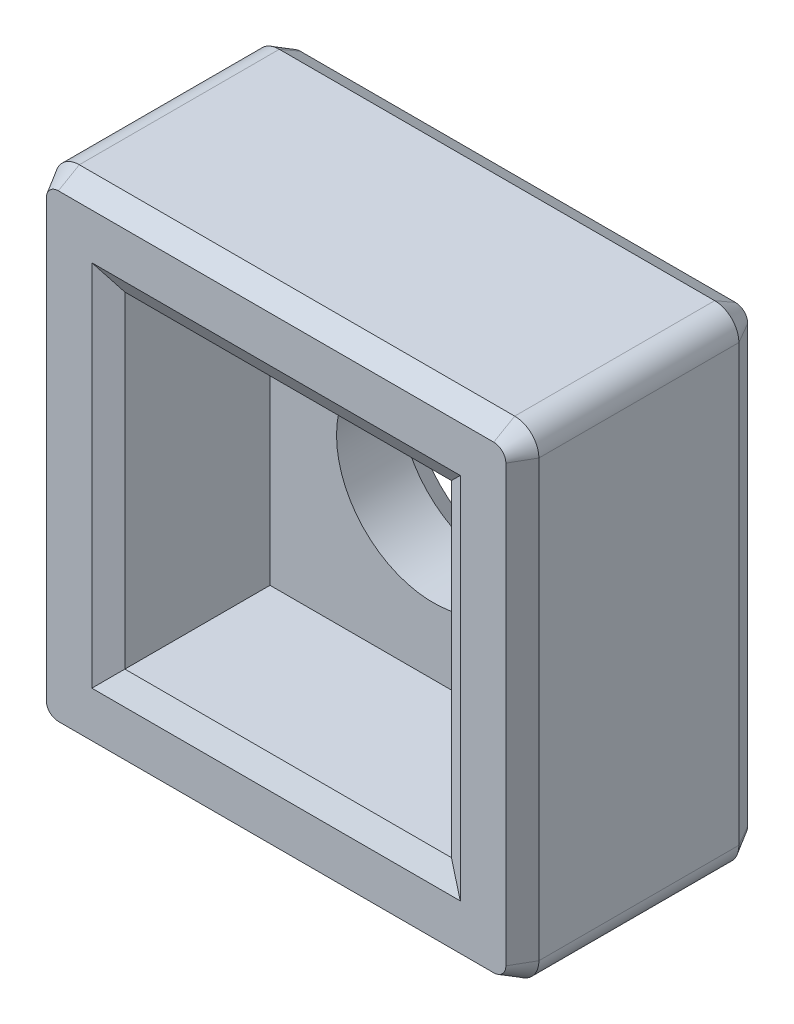
SolidWorks part; units mm, degrees
ref_plane "Front Plane" through (0, 0, 0) normal (0, 0, 1) x (1, 0, 0)
ref_plane "Top Plane" through (0, 0, 0) normal (0, 1, 0) x (1, 0, 0)
ref_plane "Right Plane" through (0, 0, 0) normal (1, 0, 0) x (0, 0, -1)
sketch "Sketch1" plane through (0, 0, 0) normal (0, 0, 1) x (1, 0, 0)
  line L0 (-4, -4) -> (4, 4) construction
  line L1 (-4, 4) -> (4, 4)
  line L2 (-4, 4) -> (-4, -4)
  line L3 (-4, -4) -> (4, -4)
  line L4 (4, 4) -> (4, -4)
  dimension "D1" = 8
extrude "Boss-Extrude1" add sketch "Sketch1" along normal blind 4
fillet "Fillet1" radius 0.4 4 edges at (-4, -4, 2) (4, -4, 2) (4, 4, 2) (-4, 4, 2)
sketch "Sketch3" plane through (0, 0, 0) normal (0, 0, -1) x (-1, 0, 0)
  circle A0 centre (0, 0) radius 1.6
  dimension "D1" = 3.2
extrude "Cut-Extrude1" cut sketch "Sketch3" against normal through all
sketch "Sketch4" plane through (0, 0, 4) normal (0, 0, 1) x (1, 0, 0)
  line L0 (2.7, 2.7) -> (-2.7, -2.7) construction
  line L1 (-2.7, 2.7) -> (2.7, 2.7)
  line L2 (-2.7, 2.7) -> (-2.7, -2.7)
  line L3 (-2.7, -2.7) -> (2.7, -2.7)
  line L4 (2.7, 2.7) -> (2.7, -2.7)
  circle A0 centre (0, 0) radius 1.6 construction
  circle A1 centre (0, 0) radius 1.6
  dimension "D1" = 5.4
extrude "Cut-Extrude2" cut sketch "Sketch4" against normal blind 2.6
chamfer "Chamfer1" distance 0.2 angle 60 21 edges at (0, -4, 0) (4, 0, 0) (0, 4, 0) (-4, 0, 0) (-1.6, 0, 0) (0, 4, 4) (4, 0, 4) (0, -4, 4) (-4, 0, 4) (0, -2.7, 4) (2.7, 0, 4) (0, 2.7, 4) (-2.7, 0, 4) (3.8828, -3.8828, 0) (3.8828, 3.8828, 0) (-3.8828, 3.8828, 0) (-3.8828, -3.8828, 0) (-3.8828, 3.8828, 4) (3.8828, 3.8828, 4) (3.8828, -3.8828, 4) (-3.8828, -3.8828, 4)
